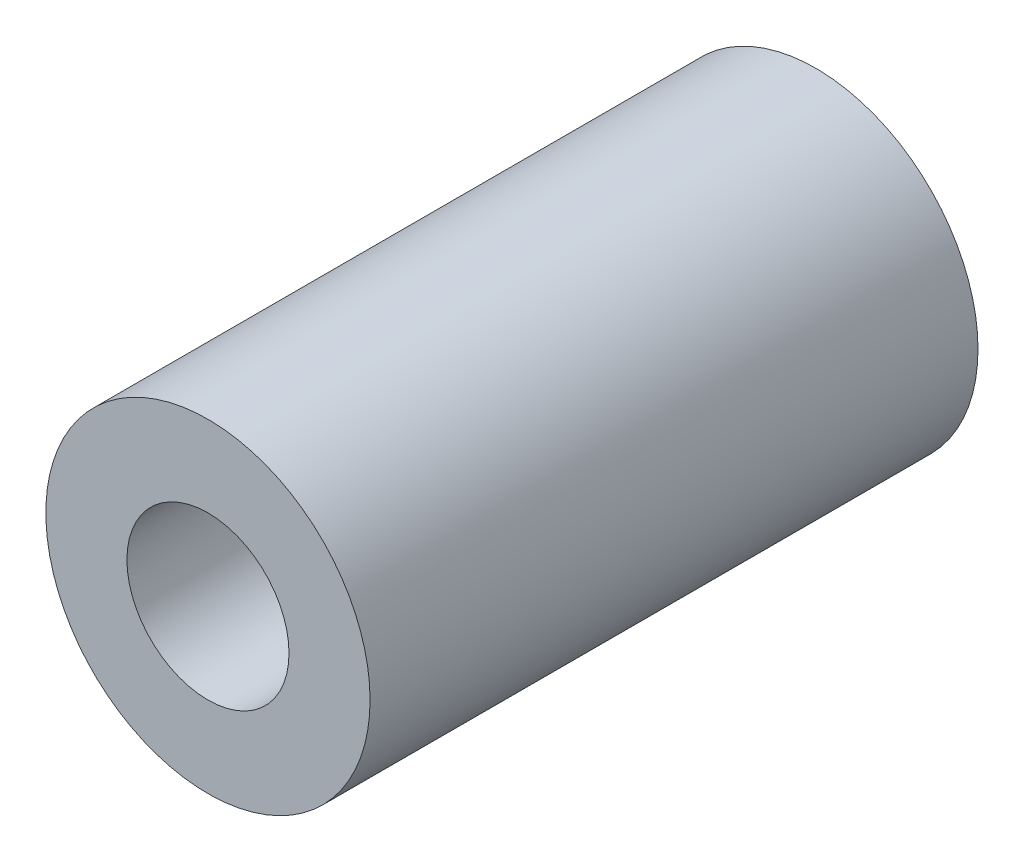
SolidWorks part; units mm, degrees
ref_plane "Front Plane" through (0, 0, 0) normal (0, 0, 1) x (1, 0, 0)
ref_plane "Top Plane" through (0, 0, 0) normal (0, 1, 0) x (1, 0, 0)
ref_plane "Right Plane" through (0, 0, 0) normal (1, 0, 0) x (0, 0, -1)
sketch "Sketch1" plane through (0, 0, 0) normal (0, 0, 1) x (1, 0, 0)
  circle A0 centre (0, 0) radius 8
  circle A1 centre (0, 0) radius 4
  dimension "D1" = 16
  dimension "D2" = 8
extrude "Boss-Extrude1" add sketch "Sketch1" along normal blind 30
